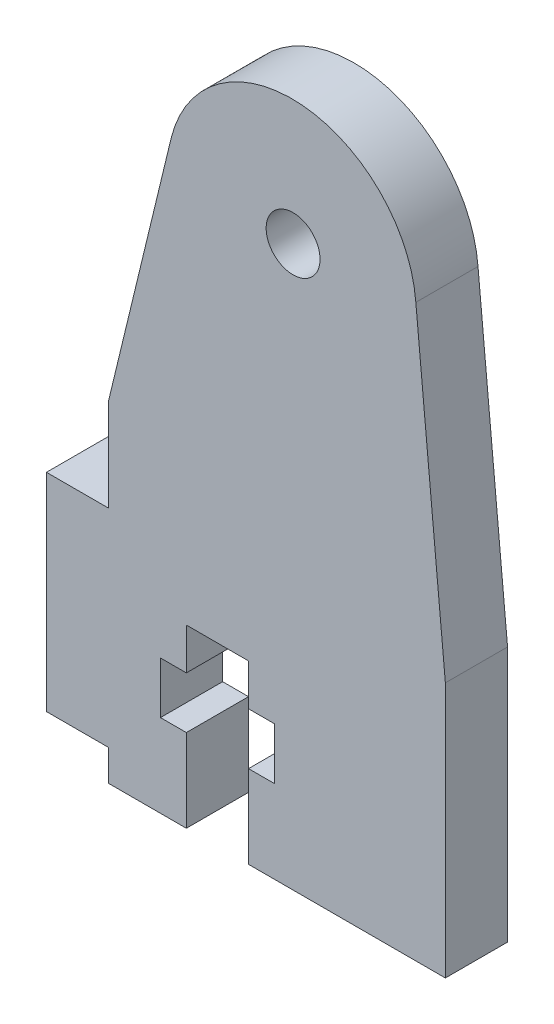
SolidWorks part; units mm, degrees
ref_plane "Front Plane" through (0, 0, 0) normal (0, 0, 1) x (1, 0, 0)
ref_plane "Top Plane" through (0, 0, 0) normal (0, 1, 0) x (1, 0, 0)
ref_plane "Right Plane" through (0, 0, 0) normal (1, 0, 0) x (0, 0, -1)
sketch "Model" plane through (0, 0, 0) normal (0, 0, 1) x (1, 0, 0)
  line L0 (48.6236, 20.4811) -> (39.1264, 20.4811)
  line L1 (32.3764, 20.4885) -> (36.1264, 20.4885)
  line L2 (29.3764, 31.9885) -> (29.3764, 21.9885)
  line L3 (32.3764, 36.4885) -> (35.3952, 48.9686)
  line L4 (48.6236, 20.4811) -> (48.6236, 32.8147)
  line L5 (32.3764, 31.9885) -> (32.3764, 36.4885)
  line L6 (29.3764, 31.9885) -> (32.3764, 31.9885)
  line L7 (39.1264, 24.4811) -> (39.1264, 20.4811)
  line L8 (40.3764, 24.4811) -> (39.1264, 24.4811)
  line L9 (40.3764, 26.9811) -> (40.3764, 24.4811)
  line L10 (39.1264, 26.9811) -> (40.3764, 26.9811)
  line L11 (39.1264, 28.9811) -> (39.1264, 26.9811)
  line L12 (36.1264, 28.9811) -> (39.1264, 28.9811)
  line L13 (36.1264, 26.9811) -> (36.1264, 28.9811)
  line L14 (34.8764, 26.9811) -> (36.1264, 26.9811)
  line L15 (34.8764, 24.4885) -> (34.8764, 26.9811)
  line L16 (36.1264, 24.4885) -> (34.8764, 24.4885)
  line L17 (36.1264, 20.4885) -> (36.1264, 24.4885)
  line L18 (48.6236, 32.8147) -> (47.1982, 48)
  line L19 (32.3764, 21.9885) -> (29.3764, 21.9885)
  line L20 (32.3764, 20.4885) -> (32.3764, 21.9885)
  circle A0 centre (41.2764, 47.4885) radius 1.3
  arc A1 (47.1982, 48) -> (35.3952, 48.9686) centre (41.2175, 47.5189) ccw
  dimension "D1" = 3
  dimension "D2" = 10
  dimension "D3" = 3
  dimension "D4" = 3.75
  dimension "D5" = 3
extrude "Boss-Extrude1" add sketch "Model" along normal blind 3
